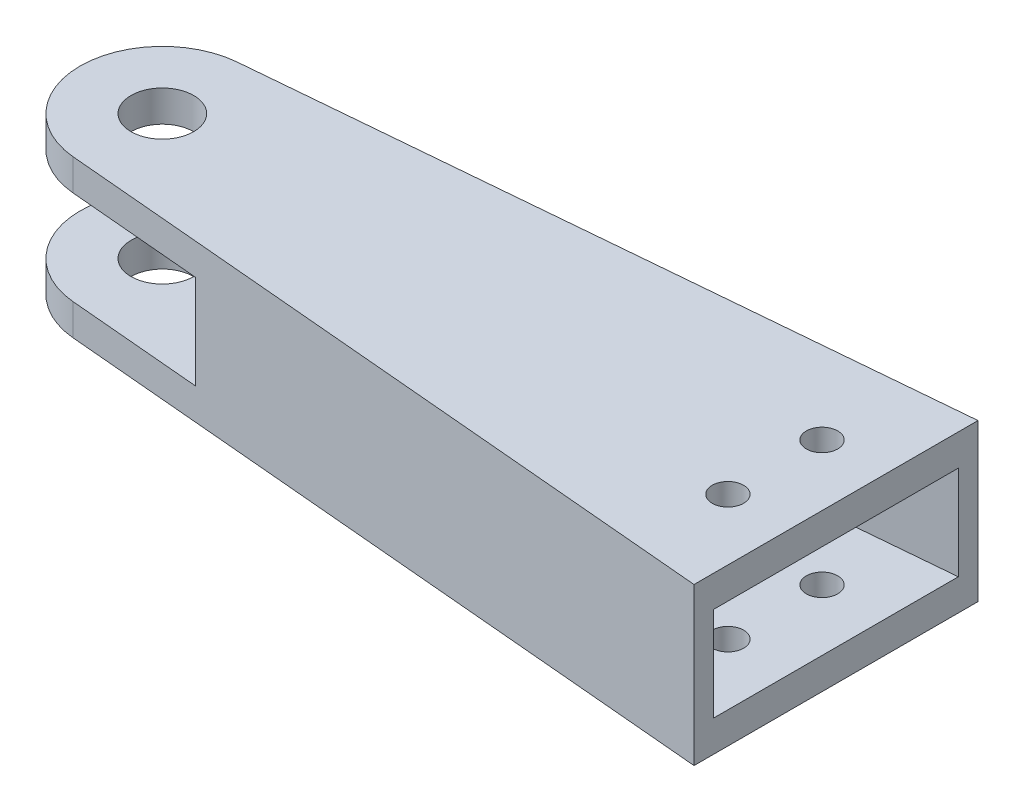
SolidWorks part; units mm, degrees
ref_plane "Front" through (0, 0, 0) normal (0, 0, 1) x (1, 0, 0)
ref_plane "Top" through (0, 0, 0) normal (0, 1, 0) x (1, 0, 0)
ref_plane "Right" through (0, 0, 0) normal (1, 0, 0) x (0, 0, -1)
sketch "Sketch1" plane through (0, 0, 0) normal (0, 1, 0) x (1, 0, 0)
  line L0 (0, 0) -> (0, 20) construction
  line L1 (-25, 20) -> (25, 20)
  line L2 (-161.6019, 7.9692) -> (-25, 20)
  line L3 (25, 20) -> (161.6242, 8.9708)
  line L4 (-160.9, 0) -> (160.9, 0) construction
  line L5 (-161.6019, -7.9692) -> (-25, -20)
  line L6 (-25, -20) -> (25, -20)
  line L7 (25, -20) -> (161.6242, -8.9708)
  line L8 (-75, -25) -> (-75, 25)
  line L9 (-95, -25) -> (95, -25)
  line L10 (-95, -25) -> (-95, 25)
  line L11 (-95, 25) -> (95, 25)
  line L12 (95, -25) -> (95, 25)
  line L13 (-95, -25) -> (95, 25) construction
  line L14 (-95, 25) -> (95, -25) construction
  line L15 (25.1007, -22.5) -> (161.8253, -11.4627)
  line L16 (-25.1099, -22.5) -> (25.1007, -22.5)
  line L17 (-161.8212, -10.4595) -> (-25.1099, -22.5)
  line L18 (-161.8212, 10.4595) -> (-25.1099, 22.5)
  line L19 (-25.1099, 22.5) -> (25.1007, 22.5)
  line L20 (25.1007, 22.5) -> (161.8253, 11.4627)
  circle A0 centre (0, 0) radius 4
  circle A1 centre (-160.9, 0) radius 4
  circle A2 centre (160.9, 0) radius 4
  circle A3 centre (160.9, 0) radius 9
  arc A4 (-161.6019, 7.9692) -> (-161.6019, -7.9692) centre (-160.9, 0) ccw
  circle A5 centre (-160.9, 0) radius 8 construction
  arc A6 (-161.8212, 10.4595) -> (-161.8212, -10.4595) centre (-160.9, 0) ccw
  dimension "D1" = 8
  dimension "D2" = 8
  dimension "D3" = 8
  dimension "D6" = 160.9
  dimension "D7" = 160.9
  dimension "D8" = 20
  dimension "D9" = 50
  dimension "D10" = 50
  dimension "D11" = 190
  dimension "D12" = 20
  dimension "D4" = 5
  dimension "D5" = 4
  dimension "D13" = 2.5
extrude "Boss-Extrude1" add sketch "Sketch1" along normal blind 4 contours L10 L5 L8 L2 | A4 L5 L10 L2 | A4 A1 | L18 A6 L17 L10 L5 A4 L2 | L10 L17 L8 L5 | L18 L10 L2 L8
ref_plane "Plane1" through (0, 16, 0) normal (0, 1, 0) x (1, 0, 0)
sketch "Sketch2" plane through (0, 16, 0) normal (0, 1, 0) x (1, 0, 0)
  line L3 (-75, 18.1061) -> (-161.8212, 10.4595)
  line L4 (-75, 18.1061) -> (-161.8212, 10.4595)
  line L5 (-75, -18.1061) -> (-75, 18.1061)
  line L8 (-75, -18.1061) -> (-75, 18.1061)
  line L9 (-161.8212, -10.4595) -> (-75, -18.1061)
  line L10 (-161.8212, -10.4595) -> (-75, -18.1061)
  circle A0 centre (-160.9, 0) radius 4 construction
  arc A1 (-161.8212, 10.4595) -> (-161.8212, -10.4595) centre (-160.9, 0) ccw
  circle A3 centre (-160.9, 0) radius 4
  arc A5 (-161.8212, 10.4595) -> (-161.8212, -10.4595) centre (-160.9, 0) ccw
  dimension "D1" = 0
extrude "Boss-Extrude2" add sketch "Sketch2" along normal blind 4 separate body
sketch "Sketch5" plane through (0, 4, 0) normal (0, 1, 0) x (1, 0, 0)
  line L0 (-75, 18.1061) -> (-161.8212, 10.4595) construction
  line L1 (-161.8212, -10.4595) -> (-75, -18.1061) construction
  line L2 (-75, 18.1061) -> (-144.7301, 11.9648)
  line L3 (-144.7301, -11.9648) -> (-75, -18.1061)
  line L4 (-74.7807, 15.6157) -> (-144.5108, 9.4744)
  line L5 (-144.5108, -9.4744) -> (-74.7807, -15.6157)
  line L6 (-144.7301, 11.9648) -> (-144.5108, 9.4744)
  line L7 (-75, -18.1061) -> (-75, 18.1061) construction
  line L8 (-75, -18.1061) -> (-75, 18.1061)
  line L9 (-144.5108, -9.4744) -> (-144.7301, -11.9648)
  line L10 (-75, 18.1061) -> (-161.8212, 10.4595) construction
  line L11 (-74.7807, 15.6157) -> (-161.6019, 7.9692) construction
  line L12 (-161.6019, -7.9692) -> (-74.7807, -15.6157) construction
  line L13 (-161.8212, -10.4595) -> (-75, -18.1061) construction
  line M4 (-75, 18.1061) -> (-161.8212, 10.4595)
  line M6 (-161.8212, -10.4595) -> (-75, -18.1061)
  line M7 (-75, -18.1061) -> (-75, 18.1061)
  dimension "D2" = 70
  dimension "D3" = 70
  dimension "D1" = 2.5
extrude "Boss-Extrude5" add sketch "Sketch5" along normal up to surface (12 mm away) contours L5 L9 M6 M7 | L6 L4 M4 M7 up to face at (-120.8053, 16, 0)
sketch "Sketch6" plane through (0, 0, 0) normal (0, -1, 0) x (-1, 0, 0)
  line L0 (74.8, 18.1237) -> (74.8, -18.0884) construction
  circle A0 centre (82.8, -5.9824) radius 2
  circle A1 centre (82.8, 6.0176) radius 2
  dimension "D1" = 4
  dimension "D2" = 4
  dimension "D3" = 8
  dimension "D4" = 6
  dimension "D5" = 6
extrude "Cut-Extrude1" cut sketch "Sketch6" against normal through all
sketch "Sketch7" plane through (0, 4, 0) normal (0, 1, 0) x (1, 0, 0)
  line L0 (-144.5108, 9.4744) -> (-144.5108, -9.4744)
  line L1 (-144.5108, -9.4744) -> (-95, -13.8349)
  line L2 (-144.5108, -9.4744) -> (-75, -15.5964) construction
  line L3 (-95, -13.8349) -> (-95, 13.8349)
  line L4 (-75, 15.5964) -> (-144.5108, 9.4744) construction
  line L5 (-95, 13.8349) -> (-144.5108, 9.4744)
  line L7 (-75, -15.5964) -> (-75, 15.5964) construction
  dimension "D1" = 20
extrude "Boss-Extrude6" add sketch "Sketch7" along normal up to surface (12 mm away) up to face at (-82.8, 16, 7.9824)
